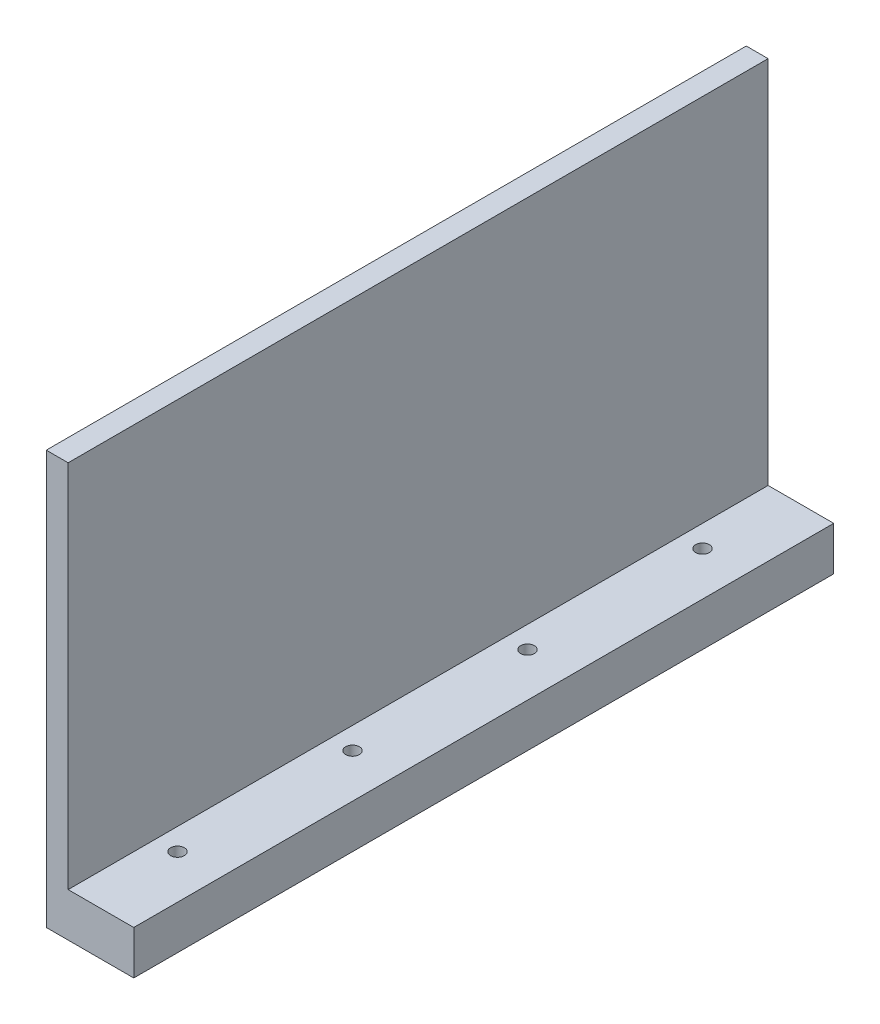
SolidWorks part; units mm, degrees
ref_plane "Front Plane" through (0, 0, 0) normal (0, 0, 1) x (1, 0, 0)
ref_plane "Top Plane" through (0, 0, 0) normal (0, 1, 0) x (1, 0, 0)
ref_plane "Right Plane" through (0, 0, 0) normal (1, 0, 0) x (0, 0, -1)
sketch "Sketch1" plane through (0, 0, 0) normal (0, 1, 0) x (1, 0, 0)
  line L1 (-6.35, -50.8) -> (6.35, -50.8)
  line L2 (-6.35, -50.8) -> (-6.35, 50.8)
  line L3 (-6.35, 50.8) -> (6.35, 50.8)
  line L4 (6.35, -50.8) -> (6.35, 50.8)
  line L5 (-6.35, -50.8) -> (6.35, 50.8) construction
  line L6 (-6.35, 50.8) -> (6.35, -50.8) construction
  point P0 (0, 0)
  dimension "D1" = 101.6
  dimension "D2" = 12.7
extrude "Boss-Extrude1" add sketch "Sketch1" along normal blind 60
sketch "Sketch2" plane through (0, 60, 0) normal (0, 1, 0) x (1, 0, 0)
  line L0 (-6.35, -50.8) -> (6.35, -50.8) construction
  line L1 (6.35, 50.8) -> (-3.175, 50.8)
  line L2 (6.35, 50.8) -> (6.35, -50.8)
  line L3 (6.35, -50.8) -> (-3.175, -50.8)
  line L4 (-3.175, 50.8) -> (-3.175, -50.8)
  line L5 (-6.35, 50.8) -> (-6.35, -50.8) construction
  dimension "D1" = 3.175
extrude "Cut-Extrude1" cut sketch "Sketch2" against normal offset from surface (53.65 mm away) 6.35 up to face at (0, 0, 0)
sketch "Sketch3" plane through (0, 6.35, 0) normal (0, 1, 0) x (1, 0, 0)
  line L0 (6.35, 50.8) -> (-3.175, 50.8) construction
  line L1 (6.35, 50.8) -> (-6.35, 50.8) construction
  circle A0 centre (0, 38.1) radius 1
  circle A5 centre (0, 12.7) radius 1
  circle A6 centre (0, -12.7) radius 1
  circle A7 centre (0, -38.1) radius 1
  point P15 (0, 50.8)
  dimension "D1" = 2
  dimension "D2" = 12.7
  dimension "D3" = 4
extrude "Cut-Extrude2" cut sketch "Sketch3" against normal through all
equation "\"D1@Sketch3\"=2mm"
equation "\"D1@Boss-Extrude1\"=60mm"
